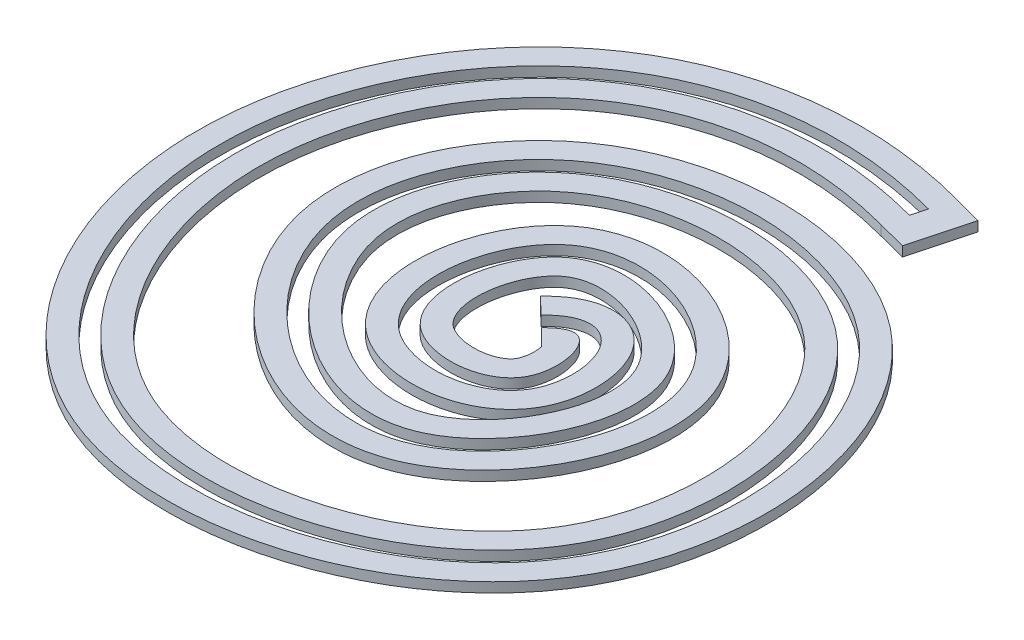
SolidWorks part; units mm, degrees
ref_plane "Front" through (0, 0, 0) normal (0, 0, 1) x (1, 0, 0)
ref_plane "Top" through (0, 0, 0) normal (0, 1, 0) x (1, 0, 0)
ref_plane "Right" through (0, 0, 0) normal (1, 0, 0) x (0, 0, -1)
sketch "Sketch1" plane through (0, 0, 0) normal (0, 1, 0) x (1, 0, 0)
  line L0 (52.0576, 154.8899) -> (61.3707, 152.3969)
  line L1 (61.3707, 152.3969) -> (56.217, 133.144)
  line L2 (56.217, 133.144) -> (46.886, 135.5701)
  line L4 (50.1182, 147.6449) -> (48.8253, 142.815)
  line L5 (11.8297, 60.5705) -> (17.2373, 55.3736)
  line L6 (20.8424, 51.909) -> (26.15, 46.6096)
  spline S0 degree 3 poles (49.4718, 145.23) (-30.2733, 166.5764) (-112.3312, 71.8665) (-35.0268, -70.2582) (115.5296, -27.5007) (94.3996, 119.5677) (-21.3453, 121.4299) (-58.4781, 36.7709) (30.4595, -32.2531) (80.7334, 65.6366) (-5.0858, 98.5715) (-16.1014, 21.0699) (47.6945, 24.782) (32.7583, 67.9161) (19.0398, 53.6413) knots 0 0 0 0 0.162272 0.275592 0.397602 0.509296 0.604259 0.663356 0.751594 0.820646 0.877922 0.927334 0.963397 1 1 1 1
  spline S1 degree 1 poles (50.1182, 147.6449) (17.2373, 55.3736) knots 0 0 1 1 construction
  spline S2 degree 3 poles (50.1182, 147.6449) (49.1497, 147.9042) (47.1977, 148.4065) (43.354, 149.3151) (38.6076, 150.2875) (33.0239, 151.1943) (25.7242, 152.0663) (16.8788, 152.5384) (6.7236, 152.1645) (-2.9576, 150.8988) (-15.2139, 148.0887) (-29.2735, 142.598) (-44.0104, 133.2641) (-56.5097, 121.6153) (-66.6846, 108.0799) (-77.044, 88.0775) (-82.4542, 65.9688) (-82.5472, 43.3752) (-79.1789, 21.0669) (-70.9853, 0.0094) (-58.5564, -18.1219) (-47.2548, -29.8262) (-34.1293, -39.2065) (-19.2803, -45.7661) (-3.15, -49.2084) (19.2036, -49.9369) (41.6938, -45.1323) (62.0038, -35.2866) (75.5587, -25.4796) (84.9505, -15.3745) (91.0071, -6.1742) (95.9745, 3.7083) (100.1701, 17.0625) (102.0908, 33.9717) (100.9861, 51.0535) (96.926, 67.6047) (89.9618, 82.9173) (81.7667, 94.0379) (73.7938, 101.5741) (64.8875, 108.05) (52.3332, 114.0624) (35.8813, 117.9735) (18.906, 118.5565) (2.2594, 115.769) (-10.6202, 110.573) (-19.8806, 104.6508) (-28.2803, 97.5211) (-36.8444, 86.6173) (-43.2792, 71.3197) (-44.7532, 57.5281) (-43.1545, 46.369) (-39.6076, 35.396) (-32.0409, 22.4615) (-19.2687, 9.2706) (-4.0426, -0.4244) (9.7233, -4.5607) (20.7826, -4.7868) (28.9249, -3.2227) (36.6545, 0.2823) (46.0029, 7.1202) (55.5878, 18.9016) (61.241, 33.0977) (62.6117, 44.8265) (61.831, 53.5228) (58.9828, 61.8261) (53.8842, 69.2482) (47.1377, 75.4783) (36.5722, 82.0027) (24.5679, 85.447) (12.8575, 84.7678) (6.0644, 82.3312) (1.2565, 78.9872) (-2.9462, 74.7925) (-7.053, 68.3127) (-10.1079, 59.3395) (-11.1592, 49.8964) (-10.004, 40.6931) (-6.9358, 33.8323) (-3.0382, 29.297) (0.6422, 26.5454) (4.8397, 24.5624) (10.8956, 22.8661) (18.9335, 22.5007) (26.6008, 24.5254) (31.8602, 27.7561) (35.1575, 31.0283) (37.5289, 35.2201) (39.1647, 41.49) (38.9308, 48.0959) (37.0278, 53.9436) (34.7149, 57.678) (31.8561, 59.9442) (28.9956, 60.8231) (26.6792, 60.9012) (24.3133, 60.3794) (21.9603, 59.2942) (19.999, 57.9297) (18.4333, 56.5725) (17.6224, 55.7744) (17.2373, 55.3736) knots 0 0 0 0 0.001953 0.003906 0.007812 0.011719 0.015625 0.023438 0.03125 0.039062 0.046875 0.0625 0.078125 0.09375 0.109375 0.125 0.15625 0.171875 0.1875 0.21875 0.234375 0.25 0.265625 0.28125 0.296875 0.3125 0.34375 0.359375 0.375 0.390625 0.398438 0.40625 0.421875 0.4375 0.453125 0.46875 0.484375 0.5 0.507812 0.515625 0.53125 0.546875 0.5625 0.578125 0.59375 0.601562 0.609375 0.625 0.640625 0.65625 0.664062 0.671875 0.6875 0.703125 0.71875 0.734375 0.742188 0.75 0.757812 0.765625 0.78125 0.796875 0.804688 0.8125 0.820312 0.828125 0.835938 0.84375 0.859375 0.867188 0.875 0.878906 0.882812 0.890625 0.898438 0.90625 0.914062 0.921875 0.925781 0.929688 0.933594 0.9375 0.945312 0.953125 0.957031 0.960938 0.964844 0.96875 0.976562 0.980469 0.984375 0.988281 0.990234 0.992188 0.994141 0.996094 0.998047 0.999023 1 1 1 1
  spline S3 degree 1 poles (48.8253, 142.815) (20.8424, 51.909) knots 0 0 1 1 construction
  spline S4 degree 3 poles (48.8253, 142.815) (47.8882, 143.0658) (45.9988, 143.552) (42.2837, 144.4302) (37.7024, 145.3687) (32.324, 146.2421) (25.3068, 147.0802) (16.8295, 147.5319) (7.1339, 147.174) (-2.078, 145.9691) (-13.7076, 143.3018) (-27.0066, 138.1062) (-40.9351, 129.2848) (-52.7688, 118.2589) (-62.4284, 105.4121) (-72.2895, 86.3772) (-77.4525, 65.2828) (-77.5411, 43.7501) (-74.3243, 22.4266) (-64.523, -2.7477) (-48.0751, -23.0928) (-31.6143, -34.8426) (-17.76, -40.9651) (-2.5605, -44.2171) (18.6619, -44.9146) (40.1347, -40.3287) (59.4405, -30.9647) (72.2403, -21.6938) (82.8014, -10.3374) (90.5128, 3.0196) (95.2437, 18.0883) (97.0665, 34.0849) (96.0181, 50.2944) (92.1697, 65.9744) (85.6038, 80.3884) (76.4342, 92.8375) (64.722, 102.5779) (50.6711, 109.3048) (35.2174, 112.9853) (19.2268, 113.5344) (3.6027, 110.9101) (-10.7743, 105.1104) (-23.0317, 96.0927) (-32.4918, 84.036) (-38.3761, 70.0289) (-39.6968, 57.5329) (-38.2638, 47.5203) (-35.0509, 37.5569) (-28.0402, 25.5347) (-16.0663, 13.1671) (-1.8673, 4.1445) (10.6461, 0.4214) (20.3808, 0.2356) (27.397, 1.5874) (34.0726, 4.6072) (42.4325, 10.7009) (51.2147, 21.4692) (56.3659, 34.4616) (57.5782, 44.924) (56.8827, 52.5069) (54.4694, 59.5347) (50.1065, 65.9077) (44.1093, 71.463) (36.974, 75.8717) (29.1977, 78.8782) (21.3012, 80.2465) (13.8114, 79.7897) (8.299, 77.787) (4.4991, 75.1465) (1.0581, 71.7246) (-2.485, 66.1732) (-5.1906, 58.2433) (-6.1153, 49.8916) (-5.0971, 41.9789) (-2.0833, 35.3346) (2.908, 30.629) (10.2426, 27.9231) (18.4389, 27.5476) (24.742, 29.2516) (28.7633, 31.738) (31.1498, 34.1276) (32.8128, 37.0475) (33.785, 40.6842) (34.0192, 44.6306) (33.539, 48.5) (32.4221, 51.8868) (30.815, 54.3913) (29.0567, 55.6817) (27.581, 55.9511) (25.9724, 55.6223) (24.7483, 55.0696) (23.6467, 54.3706) (22.7648, 53.7085) (21.9851, 53.0325) (21.3419, 52.4192) (21.0053, 52.0785) (20.8424, 51.909) knots 0 0 0 0 0.001953 0.003906 0.007812 0.011719 0.015625 0.023438 0.03125 0.039062 0.046875 0.0625 0.078125 0.09375 0.109375 0.125 0.15625 0.171875 0.1875 0.21875 0.25 0.265625 0.28125 0.296875 0.3125 0.34375 0.359375 0.375 0.390625 0.40625 0.421875 0.4375 0.453125 0.46875 0.484375 0.5 0.515625 0.53125 0.546875 0.5625 0.578125 0.59375 0.609375 0.625 0.640625 0.65625 0.664062 0.671875 0.6875 0.703125 0.71875 0.734375 0.742188 0.75 0.757812 0.765625 0.78125 0.796875 0.804688 0.8125 0.820312 0.828125 0.835938 0.84375 0.851562 0.859375 0.867188 0.875 0.878906 0.882812 0.890625 0.898438 0.90625 0.914062 0.921875 0.929688 0.9375 0.945312 0.953125 0.957031 0.960938 0.964844 0.96875 0.972656 0.976562 0.980469 0.984375 0.988281 0.992188 0.994141 0.996094 0.99707 0.998047 0.999023 0.999512 1 1 1 1
  spline S5 degree 1 poles (52.0576, 154.8899) (11.8297, 60.5705) knots 0 0 1 1 construction
  spline S6 degree 3 poles (52.0576, 154.8899) (51.042, 155.1617) (48.9961, 155.6882) (44.9594, 156.6424) (39.9654, 157.6657) (34.0738, 158.6227) (26.3504, 159.5456) (16.9528, 160.0482) (6.1082, 159.6501) (-4.277, 158.2934) (-17.4733, 155.269) (-32.6738, 149.3357) (-48.6232, 139.233) (-62.1211, 126.65) (-73.0691, 112.0817) (-84.1757, 90.628) (-89.9568, 66.9979) (-90.0564, 42.8127) (-86.4606, 19.0278) (-77.739, -3.4104) (-64.4086, -22.8669) (-52.2011, -35.5233) (-40.273, -44.0419) (-29.7511, -49.3684) (-18.6282, -53.5841) (-4.0382, -56.6965) (14.0048, -57.2782) (32.023, -54.8969) (49.4866, -49.6973) (65.8492, -41.7699) (80.5336, -31.1551) (90.822, -20.1013) (97.5189, -9.9296) (102.9918, 0.9639) (107.5579, 15.5273) (110.3145, 39.8911) (106.5794, 64.4981) (96.4966, 86.7073) (87.4811, 98.961) (78.6033, 107.3562) (68.6565, 114.5867) (54.8236, 121.1954) (36.878, 125.4565) (18.4242, 126.0903) (0.2455, 123.0543) (-13.9867, 117.3262) (-24.3413, 110.7086) (-33.7914, 102.6873) (-43.3717, 90.4847) (-49.4259, 76.1319) (-51.6531, 63.8089) (-51.8769, 54.3027) (-50.4902, 44.6422) (-47.4552, 35.2749) (-43.0807, 26.4398) (-35.7146, 15.4435) (-24.0733, 3.4285) (-10.0962, -5.4978) (2.0744, -10.1247) (11.601, -12.1075) (21.3902, -12.3192) (29.5621, -10.7539) (35.9, -8.3179) (41.8652, -5.2127) (48.6558, -0.2405) (55.674, 7.0762) (61.4924, 15.4536) (65.9819, 24.6516) (68.9576, 34.4601) (70.1638, 44.6758) (69.3976, 53.3325) (67.5159, 60.1316) (65.4162, 65.1087) (62.6354, 69.7924) (58.2486, 75.448) (51.6768, 81.5063) (42.5742, 87.124) (32.6267, 90.9798) (22.1491, 92.8264) (13.2149, 92.3353) (6.1961, 90.3778) (1.133, 88.049) (-3.6074, 84.7477) (-7.6171, 80.7333) (-10.9307, 76.2442) (-14.5032, 69.7665) (-17.4829, 60.9833) (-18.7261, 49.9048) (-17.5882, 40.6176) (-15.0272, 33.4621) (-12.1471, 28.373) (-8.8727, 24.5582) (-5.6978, 21.8969) (-2.2941, 19.6253) (2.2322, 17.4914) (9.8278, 15.3754) (17.7102, 15.0145) (25.4948, 16.4416) (31.17, 18.522) (36.5065, 21.7787) (40.3873, 25.6288) (42.8941, 29.4024) (44.8661, 33.5445) (46.2165, 38.7755) (46.5791, 45.035) (45.8309, 51.146) (43.9405, 57.0246) (41.1121, 61.6902) (37.6204, 65.0186) (34.2626, 67.0693) (30.2351, 68.3107) (25.9286, 68.4446) (21.8254, 67.5169) (18.1435, 65.7941) (15.3903, 63.864) (13.3264, 62.0713) (12.3161, 61.0767) (11.8297, 60.5705) knots 0 0 0 0 0.001953 0.003906 0.007812 0.011719 0.015625 0.023438 0.03125 0.039062 0.046875 0.0625 0.078125 0.09375 0.109375 0.125 0.15625 0.171875 0.1875 0.21875 0.234375 0.25 0.265625 0.273438 0.28125 0.296875 0.3125 0.328125 0.34375 0.359375 0.375 0.390625 0.398438 0.40625 0.421875 0.4375 0.46875 0.484375 0.5 0.507812 0.515625 0.53125 0.546875 0.5625 0.578125 0.59375 0.601562 0.609375 0.625 0.640625 0.648438 0.65625 0.664062 0.671875 0.679688 0.6875 0.703125 0.71875 0.726562 0.734375 0.742188 0.75 0.753906 0.757812 0.765625 0.773438 0.78125 0.789062 0.796875 0.804688 0.8125 0.816406 0.820312 0.824219 0.828125 0.835938 0.84375 0.851562 0.859375 0.867188 0.871094 0.875 0.878906 0.882812 0.886719 0.890625 0.898438 0.90625 0.914062 0.917969 0.921875 0.925781 0.927734 0.929688 0.933594 0.9375 0.945312 0.949219 0.953125 0.957031 0.960938 0.962891 0.964844 0.96875 0.972656 0.976562 0.980469 0.984375 0.986328 0.988281 0.990234 0.992188 0.994141 0.996094 0.998047 0.999023 1 1 1 1
  spline S7 degree 1 poles (46.886, 135.5701) (26.15, 46.6096) knots 0 0 1 1 construction
  spline S8 degree 3 poles (46.886, 135.5701) (46.0169, 135.8027) (44.2642, 136.2541) (40.8241, 137.0698) (36.5899, 137.9435) (31.6327, 138.7609) (25.1823, 139.5544) (17.4212, 140.0079) (8.5883, 139.7485) (0.2311, 138.7402) (-10.2872, 136.4657) (-22.2849, 131.9985) (-34.8933, 124.37) (-45.7132, 114.7635) (-54.6879, 103.4707) (-64.0711, 86.5937) (-69.3737, 67.6672) (-70.2266, 48.2342) (-68.1093, 28.7791) (-61.7939, 10.1084) (-51.9054, -6.1281) (-42.903, -16.7052) (-32.5037, -25.3381) (-22.8421, -30.6631) (-14.5093, -33.6923) (-5.7117, -35.9444) (5.9391, -37.275) (20.418, -36.5177) (34.7886, -33.4751) (48.4521, -28.269) (60.8284, -21.0635) (69.6217, -13.5632) (75.5212, -6.7621) (79.3271, -1.2907) (82.4951, 4.5865) (85.9313, 13.0196) (88.6888, 24.4377) (89.4903, 38.889) (87.7927, 53.3557) (83.6763, 67.1073) (77.2923, 79.4345) (70.2358, 88.0135) (63.6646, 93.5937) (56.341, 98.3885) (45.9123, 102.902) (32.1405, 105.7279) (17.9802, 105.8439) (4.3287, 103.2265) (-7.9721, 97.9573) (-18.169, 90.1838) (-26.106, 79.8706) (-30.9953, 68.0724) (-32.0932, 57.7792) (-31.0152, 49.6736) (-28.4917, 41.4496) (-22.6578, 31.0182) (-12.3635, 19.9699) (-2.1765, 13.1398) (6.1383, 9.6556) (12.2454, 8.1143) (18.034, 7.6824) (23.4048, 8.3502) (28.3609, 10.1195) (33.4378, 13.2736) (38.2572, 17.6594) (43.968, 24.8295) (48.0568, 33.3792) (49.8135, 41.9234) (49.9094, 47.9735) (48.7861, 53.4205) (46.5095, 58.1398) (42.602, 62.8294) (37.3763, 66.9627) (31.307, 70.1615) (24.961, 72.1343) (18.9488, 72.7202) (14.7219, 72.088) (11.9433, 71.0251) (10.1421, 69.9774) (8.4985, 68.5974) (6.8229, 66.6692) (5.2778, 64.2837) (3.4851, 60.5921) (1.9343, 55.292) (1.4938, 48.7949) (2.5073, 43.1705) (4.229, 39.948) (5.6772, 38.4391) (6.6228, 37.7168) (7.7932, 36.9965) (9.6124, 36.195) (13.0947, 35.3017) (17.0058, 35.1987) (20.4492, 35.9016) (22.5927, 36.7396) (24.1532, 37.7426) (25.1403, 38.7837) (25.728, 39.771) (26.3068, 41.7347) (26.4543, 43.8) (26.3449, 45.4672) (26.2277, 46.2257) (26.15, 46.6096) knots 0 0 0 0 0.001907 0.003813 0.007627 0.01144 0.015253 0.02288 0.030507 0.038133 0.04576 0.061014 0.076267 0.09152 0.106774 0.122027 0.152534 0.167787 0.183041 0.213548 0.228801 0.244054 0.259308 0.274561 0.282188 0.289815 0.305068 0.320321 0.335575 0.350828 0.366082 0.381335 0.388962 0.396588 0.404215 0.411842 0.427095 0.442348 0.457602 0.472855 0.488109 0.503362 0.510989 0.518615 0.533869 0.549122 0.564376 0.579629 0.594882 0.610136 0.625389 0.640643 0.655896 0.663523 0.671149 0.686403 0.701656 0.71691 0.724536 0.732163 0.73979 0.747416 0.755043 0.76267 0.770297 0.777923 0.793177 0.800803 0.80843 0.816057 0.823683 0.83131 0.838937 0.846564 0.85419 0.861817 0.869444 0.873257 0.87707 0.880884 0.884697 0.88851 0.892324 0.89995 0.907577 0.915204 0.92283 0.926644 0.928551 0.930457 0.934271 0.938084 0.945711 0.949524 0.953337 0.957151 0.960964 0.964777 0.968591 0.972404 0.974311 0.976217 0.976217 0.976217 0.976217
  dimension "D1" = 200
  dimension "D2" = 2.5
  dimension "D3" = 2.5
  dimension "D4" = 10
  dimension "D5" = 10
extrude "Boss-Extrude1" add sketch "Sketch1" along normal blind 3.175 contours L6 S8 L2 L1 L0 S6 L5 S2 L4 S4
